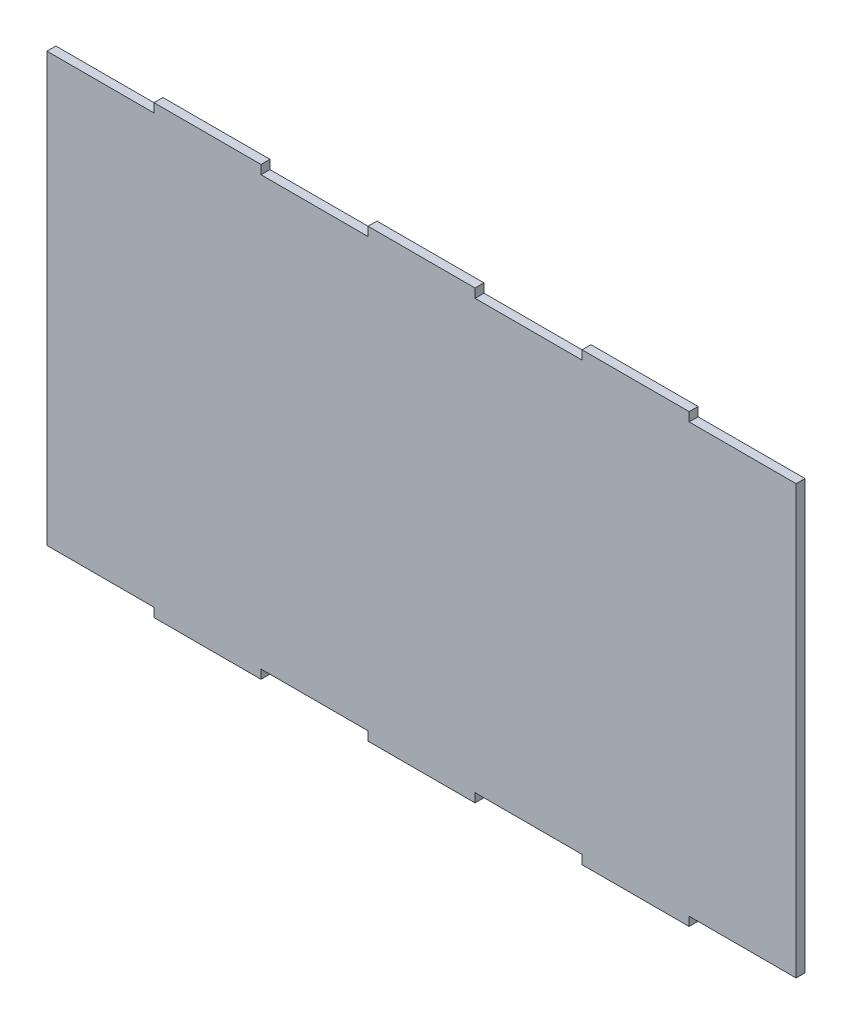
SolidWorks part; units mm, degrees
material "Contreplaqué pin"
ref_plane "Plan de face" through (0, 0, 0) normal (0, 0, 1) x (1, 0, 0)
ref_plane "Plan de dessus" through (0, 0, 0) normal (0, 1, 0) x (1, 0, 0)
ref_plane "Plan de droite" through (0, 0, 0) normal (1, 0, 0) x (0, 0, -1)
sketch "Esquisse1" plane through (0, 0, 0) normal (0, 0, 1) x (1, 0, 0)
  line L0 (0, 245) -> (60, 245)
  line L1 (60, 0) -> (120, 0)
  line L2 (0, 5) -> (0, 245)
  line L4 (420, 5) -> (420, 245)
  line L5 (60, 245) -> (60, 250)
  line L6 (60, 250) -> (120, 250)
  line L7 (120, 250) -> (120, 245)
  line L8 (120, 245) -> (180, 245)
  line L9 (180, 245) -> (180, 250)
  line L10 (180, 250) -> (240, 250)
  line L11 (240, 250) -> (240, 245)
  line L12 (240, 245) -> (300, 245)
  line L13 (300, 245) -> (300, 250)
  line L14 (300, 250) -> (360, 250)
  line L15 (360, 250) -> (360, 245)
  line L16 (360, 245) -> (420, 245)
  line L17 (300, 250) -> (360, 250)
  line L18 (0, 5) -> (60, 5)
  line L19 (60, 5) -> (60, 0)
  line L20 (60, 0) -> (120, 0)
  line L21 (120, 0) -> (120, 5)
  line L22 (120, 5) -> (180, 5)
  line L23 (180, 5) -> (180, 0)
  line L24 (180, 0) -> (240, 0)
  line L25 (240, 0) -> (240, 5)
  line L26 (240, 5) -> (300, 5)
  line L27 (300, 5) -> (300, 0)
  line L28 (300, 0) -> (360, 0)
  line L29 (360, 0) -> (360, 5)
  line L30 (360, 5) -> (420, 5)
  line L31 (180, 0) -> (240, 0)
  line L32 (300, 0) -> (360, 0)
  dimension "D1" = 250
  dimension "D2" = 420
  dimension "D3" = 5
  dimension "D4" = 5
extrude "Boss.-Extru.1" add sketch "Esquisse1" along normal blind 5 contours L29 L30 L4 L16 L15 L14 L13 L12 L11 L10 L9 L8 L7 L6 L5 L0 L2 L18 L19 L1 L21 L22 L23 L24 L25 L26 L27 L28
